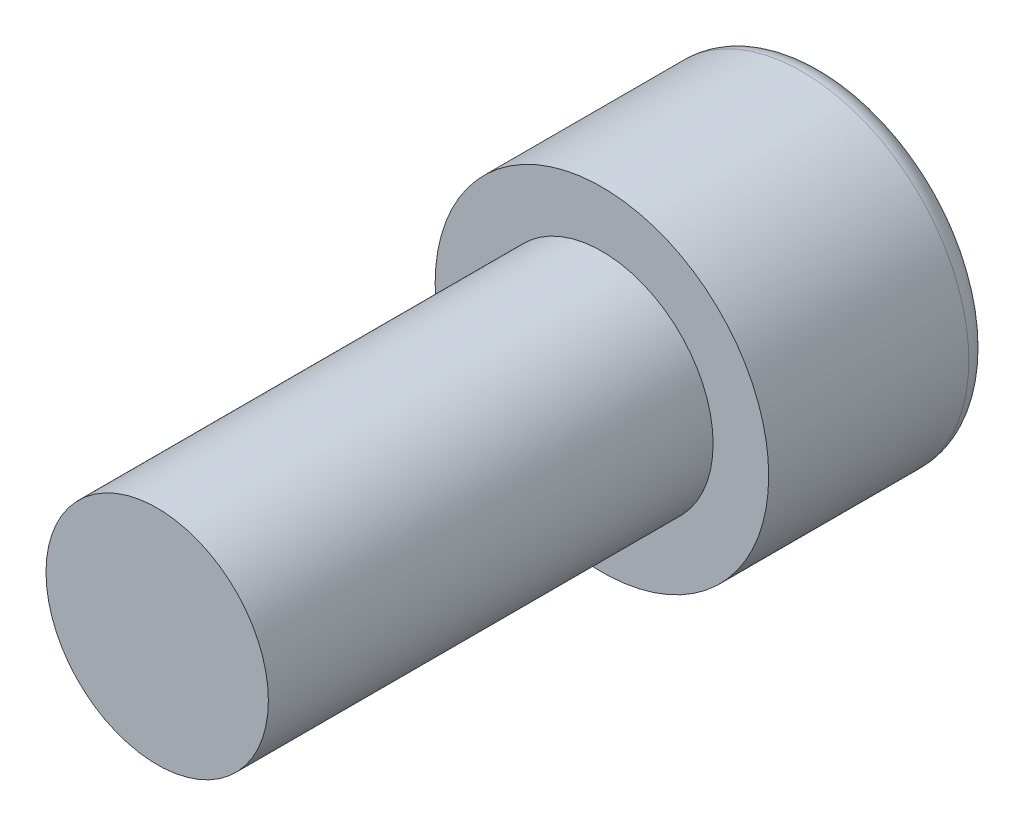
SolidWorks part; units mm, degrees
ref_plane "Front Plane" through (0, 0, 0) normal (0, 0, 1) x (1, 0, 0)
ref_plane "Top Plane" through (0, 0, 0) normal (0, 1, 0) x (1, 0, 0)
ref_plane "Right Plane" through (0, 0, 0) normal (1, 0, 0) x (0, 0, -1)
sketch "Sketch1" plane through (0, 0, 0) normal (0, 0, 1) x (1, 0, 0)
  circle A0 centre (0, 0) radius 1
  dimension "D1" = 2
extrude "Boss-Extrude1" add sketch "Sketch1" along normal blind 4
sketch "Sketch2" plane through (0, 0, 0) normal (0, 0, -1) x (-1, 0, 0)
  circle A0 centre (0, 0) radius 1.5
  dimension "D1" = 3
extrude "Boss-Extrude2" add sketch "Sketch2" along normal blind 2
fillet "Fillet1" radius 0.2 1 edges at (-1.5, 0, -2)
sketch "Sketch3" plane through (0, 0, -2) normal (0, 0, -1) x (-1, 0, 0)
  line L1 (0, -0.866) -> (0.75, -0.433)
  line L2 (0.75, -0.433) -> (0.75, 0.433)
  line L3 (0.75, 0.433) -> (0, 0.866)
  line L4 (0, 0.866) -> (-0.75, 0.433)
  line L5 (-0.75, 0.433) -> (-0.75, -0.433)
  line L6 (-0.75, -0.433) -> (0, -0.866)
  circle A0 centre (0, 0) radius 0.75 construction
  point P1 (-0.75, 0)
  dimension "D1" = 1.5
extrude "Cut-Extrude1" cut sketch "Sketch3" against normal blind 1.8
